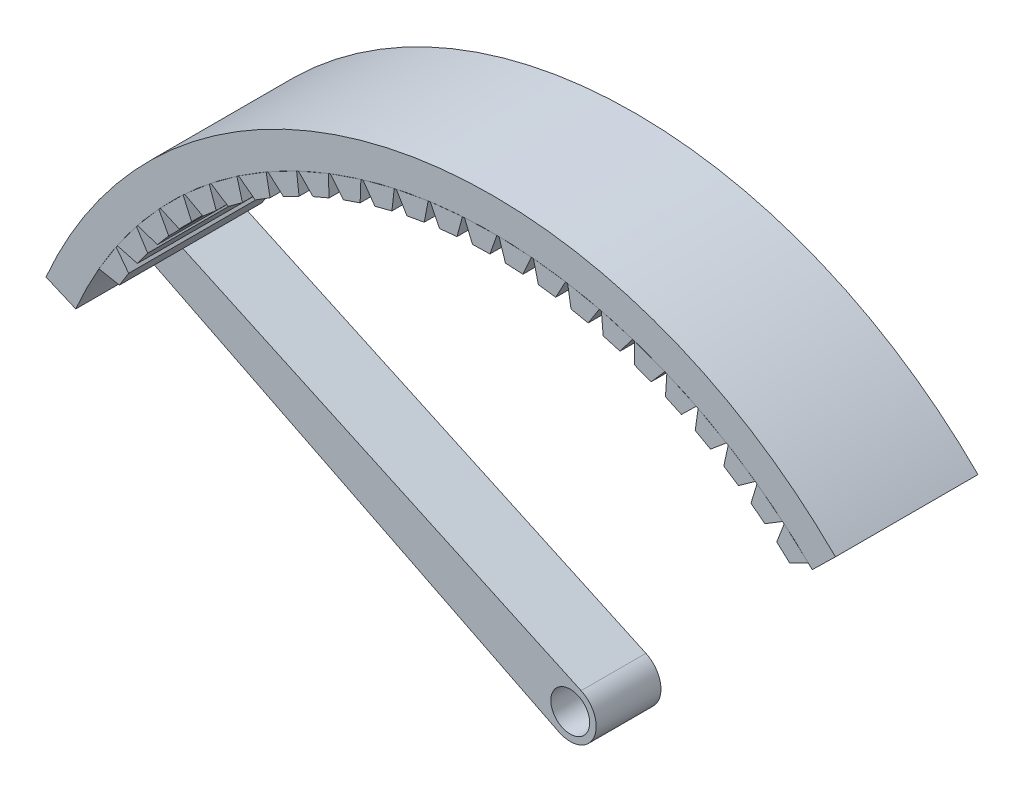
SolidWorks part; units mm, degrees
ref_plane "Front Plane" through (0, 0, 0) normal (0, 0, 1) x (1, 0, 0)
ref_plane "Top Plane" through (0, 0, 0) normal (0, 1, 0) x (1, 0, 0)
ref_plane "Right Plane" through (0, 0, 0) normal (1, 0, 0) x (0, 0, -1)
sketch "Sketch2" plane through (0, 0, 0) normal (0, 1, 0) x (1, 0, 0)
  line L1 (0, 19.1406) -> (0, 42.1406)
  line L2 (21.9625, 25.9706) -> (-21.9625, 25.9706)
  circle A0 centre (0, 19.1406) radius 23
  point P1 (0, 25.9706)
  point P7 (0, 25.9706)
  dimension "D1" = 16.17
  dimension "D2" = 46
ref_plane "Plane1" through (0, 0, -25.9706) normal (0, 0, -1) x (-1, 0, 0)
sketch "Sketch3" plane through (0, 0, -25.9706) normal (0, 0, -1) x (-1, 0, 0)
  line L0 (21.9625, 0) -> (-21.9625, 0)
  line L1 (21.9625, 0) -> (21.9625, 85)
  line L2 (-21.9625, 0) -> (-21.9625, 85)
  line L3 (21.9625, 85) -> (-21.9625, 85)
  line L4 (21.9625, 0) -> (-21.9625, 85) construction
  line L5 (-21.9625, 0) -> (21.9625, 85) construction
  line L11 (-26.4622, 69.0707) -> (-24.6744, 67.3228)
  line L12 (32.1526, 56.3278) -> (34.4493, 57.3155)
  arc A0 (-24.6744, 67.3228) -> (32.1526, 56.3278) centre (0, 42.5) cw
  arc A1 (23.9765, 17.0024) -> (8.6581, 8.5878) centre (0, 42.5) cw
  arc A2 (-26.4622, 69.0707) -> (34.4493, 57.3155) centre (0, 42.5) cw
  circle A3 centre (16.0681, 11.4063) radius 2
  point P6 (0, 42.5)
  point P10 (16.0681, 11.4063)
  point P13 (-21.9625, 69.7516)
  dimension "D2" = 5.8944
  dimension "D1" = 85
  dimension "D3" = 15.2484
extrude "Boss-Extrude1" add sketch "Sketch3" along normal blind 5 contours A2 L1 A0 L12 | A2 L2 A0 L1 | A2 L11 A0 L2
sketch "Sketch4" plane through (0, 0, -30.9706) normal (0, 0, -1) x (-1, 0, 0)
  line L0 (-22.5128, 69.2987) -> (-24.3684, 67.6233)
  line L1 (-23.4406, 68.461) -> (-22.4354, 67.3477) construction
  line L2 (-21.9328, 67.8015) -> (-22.938, 66.8939)
  line L3 (-22.938, 66.8939) -> (-24.3684, 67.6233)
  line L4 (-21.9328, 67.8015) -> (-22.5128, 69.2987)
  line L5 (-19.9474, 69.3945) -> (-20.412, 70.9315)
  line L6 (-20.412, 70.9315) -> (-22.3895, 69.4019)
  line L7 (-21.0186, 68.5659) -> (-22.3895, 69.4019)
  line L8 (-19.9474, 69.3945) -> (-21.0186, 68.5659)
  line L9 (-17.8467, 70.8321) -> (-18.1933, 72.3999)
  line L10 (-18.1933, 72.3999) -> (-20.2812, 71.025)
  line L11 (-18.9778, 70.0872) -> (-20.2812, 71.025)
  line L12 (-17.8467, 70.8321) -> (-18.9778, 70.0872)
  line L13 (-15.6429, 72.106) -> (-15.8693, 73.6956)
  line L14 (-15.8693, 73.6956) -> (-18.0557, 72.4832)
  line L15 (-16.8273, 71.4492) -> (-18.0557, 72.4832)
  line L16 (-15.6429, 72.106) -> (-16.8273, 71.4492)
  line L17 (-13.3486, 73.2087) -> (-13.4537, 74.811)
  line L18 (-13.4537, 74.811) -> (-15.7258, 73.7682)
  line L19 (-14.5796, 72.6438) -> (-15.7258, 73.7682)
  line L20 (-13.3486, 73.2087) -> (-14.5796, 72.6438)
  line L21 (-10.9773, 74.134) -> (-10.9603, 75.7396)
  line L22 (-10.9603, 75.7396) -> (-13.3051, 74.8724)
  line L23 (-12.2476, 73.6642) -> (-13.3051, 74.8724)
  line L24 (-10.9773, 74.134) -> (-12.2476, 73.6642)
  line L25 (-8.5425, 74.8765) -> (-8.4036, 76.4762)
  line L26 (-8.4036, 76.4762) -> (-10.8075, 75.7896)
  line L27 (-9.8448, 74.5046) -> (-10.8075, 75.7896)
  line L28 (-8.5425, 74.8765) -> (-9.8448, 74.5046)
  line L29 (-6.0583, 75.4319) -> (-5.7983, 77.0164)
  line L30 (-5.7983, 77.0164) -> (-8.2474, 76.5144)
  line L31 (-7.3851, 75.16) -> (-8.2474, 76.5144)
  line L32 (-6.0583, 75.4319) -> (-7.3851, 75.16)
  line L33 (-3.5391, 75.797) -> (-3.1596, 77.3571)
  line L34 (-3.1596, 77.3571) -> (-5.6397, 77.0426)
  line L35 (-4.8828, 75.6266) -> (-5.6397, 77.0426)
  line L36 (-3.5391, 75.797) -> (-4.8828, 75.6266)
  line L37 (-0.9995, 75.9696) -> (-0.5025, 77.4964)
  line L38 (-0.5025, 77.4964) -> (-2.9994, 77.3712)
  line L39 (-2.3522, 75.9018) -> (-2.9994, 77.3712)
  line L40 (-0.9995, 75.9696) -> (-2.3522, 75.9018)
  line L41 (1.5459, 75.9488) -> (2.1574, 77.4334)
  line L42 (2.1574, 77.4334) -> (-0.3417, 77.4983)
  line L43 (0.192, 75.984) -> (-0.3417, 77.4983)
  line L44 (1.5459, 75.9488) -> (0.192, 75.984)
  line L45 (4.0824, 75.7347) -> (4.8049, 77.1686)
  line L46 (4.8049, 77.1686) -> (2.3179, 77.4232)
  line L47 (2.735, 75.8726) -> (2.3179, 77.4232)
  line L48 (4.0824, 75.7347) -> (2.735, 75.8726)
  line L49 (6.5952, 75.3286) -> (7.4246, 76.7034)
  line L50 (7.4246, 76.7034) -> (4.9642, 77.1462)
  line L51 (5.2623, 75.5684) -> (4.9642, 77.1462)
  line L52 (6.5952, 75.3286) -> (5.2623, 75.5684)
  line L53 (9.07, 74.7327) -> (10.0014, 76.0406)
  line L54 (10.0014, 76.0406) -> (7.5817, 76.669)
  line L55 (7.7591, 75.0731) -> (7.5817, 76.669)
  line L56 (9.07, 74.7327) -> (7.7591, 75.0731)
  line L57 (11.4923, 73.9506) -> (12.5205, 75.1839)
  line L58 (12.5205, 75.1839) -> (10.1554, 75.9943)
  line L59 (10.2111, 74.3896) -> (10.1554, 75.9943)
  line L60 (11.4923, 73.9506) -> (10.2111, 74.3896)
  line L61 (13.8483, 72.9867) -> (14.9671, 74.1384)
  line L62 (14.9671, 74.1384) -> (12.6705, 75.126)
  line L63 (12.6041, 73.5218) -> (12.6705, 75.126)
  line L64 (13.8483, 72.9867) -> (12.6041, 73.5218)
  line L65 (16.1242, 71.8466) -> (17.3273, 72.91)
  line L66 (17.3273, 72.91) -> (15.1123, 74.0693)
  line L67 (14.9242, 72.4747) -> (15.1123, 74.0693)
  line L68 (16.1242, 71.8466) -> (14.9242, 72.4747)
  line L69 (18.3069, 70.5369) -> (19.5873, 71.5058)
  line L70 (19.5873, 71.5058) -> (17.4668, 72.83)
  line L71 (17.1581, 71.2543) -> (17.4668, 72.83)
  line L72 (18.3069, 70.5369) -> (17.1581, 71.2543)
  line L73 (20.3838, 69.0652) -> (21.7341, 69.9341)
  line L74 (21.7341, 69.9341) -> (19.7203, 71.4155)
  line L75 (19.2929, 69.8678) -> (19.7203, 71.4155)
  line L76 (20.3838, 69.0652) -> (19.2929, 69.8678)
  line L77 (22.343, 67.44) -> (23.7553, 68.2038)
  line L78 (23.7553, 68.2038) -> (21.8599, 69.8339)
  line L79 (21.3161, 68.3232) -> (21.8599, 69.8339)
  line L80 (22.343, 67.44) -> (21.3161, 68.3232)
  line L81 (24.173, 65.6707) -> (25.6393, 66.3249)
  line L82 (25.6393, 66.3249) -> (23.8732, 68.0944)
  line L83 (23.2162, 66.6293) -> (23.8732, 68.0944)
  line L84 (24.173, 65.6707) -> (23.2162, 66.6293)
  line L85 (25.8633, 63.7674) -> (27.3751, 64.3084)
  line L86 (27.3751, 64.3084) -> (25.7485, 66.2069)
  line L87 (24.9821, 64.7959) -> (25.7485, 66.2069)
  line L88 (25.8633, 63.7674) -> (24.9821, 64.7959)
  line L89 (27.4041, 61.7413) -> (28.9526, 62.1658)
  line L90 (28.9526, 62.1658) -> (27.475, 64.1824)
  line L91 (26.6036, 62.8338) -> (27.475, 64.1824)
  line L92 (27.4041, 61.7413) -> (26.6036, 62.8338)
  line L93 (28.7866, 59.6039) -> (30.3629, 59.9096)
  line L94 (30.3629, 59.9096) -> (29.0427, 62.0326)
  line L95 (28.0714, 60.7541) -> (29.0427, 62.0326)
  line L96 (28.7866, 59.6039) -> (28.0714, 60.7541)
  line L101 (29.3769, 58.5689) -> (30.4426, 59.7699) [skipped]
  line L102 (30.0027, 57.3677) -> (29.3769, 58.5689) [skipped]
  line L103 (30.0027, 57.3677) -> (31.5977, 57.5528) [skipped]
  line L104 (31.5977, 57.5528) -> (30.4426, 59.7699) [skipped]
  arc A0 (32.1526, 56.3278) -> (-24.6744, 67.3228) centre (0, 42.5) ccw construction
  point P10 (-22.4354, 67.3477)
  point P110 (0, 42.5)
  dimension "D1" = 25
extrude "Boss-Extrude2" add sketch "Sketch4" against normal blind 11 separate body
sketch "Sketch5" plane through (0, 0, -25.9706) normal (0, 0, -1) x (-1, 0, 0)
  line L0 (32.1526, 56.3278) -> (0.8951, 40.7088)
  line L1 (-0.8394, 44.318) -> (30.896, 58.9702)
  line L3 (30.896, 58.9702) -> (30.9934, 59.013)
  line L5 (30.9934, 59.013) -> (32.2384, 56.3713)
  line L6 (32.2384, 56.3713) -> (32.1526, 56.3278)
  arc A0 (-0.8394, 44.318) -> (0.8951, 40.7088) centre (0, 42.5) ccw
  circle A1 centre (0, 42.5) radius 1.5
extrude "Boss-Extrude8" add sketch "Sketch5" along normal blind 5
sketch "Sketch6" plane through (0, 0, -25.9706) normal (0, 0, 1) x (1, 0, 0)
  line L0 (26.4622, 69.0707) -> (24.6744, 67.3228)
  line L1 (-34.4493, 57.3155) -> (-32.1526, 56.3278)
  line L2 (26.4622, 69.0707) -> (24.6744, 67.3228)
  circle A0 centre (0, 42.5) radius 37.5
  circle A1 centre (0, 42.5) radius 35
extrude "Boss-Extrude9" add sketch "Sketch6" along normal blind 6
